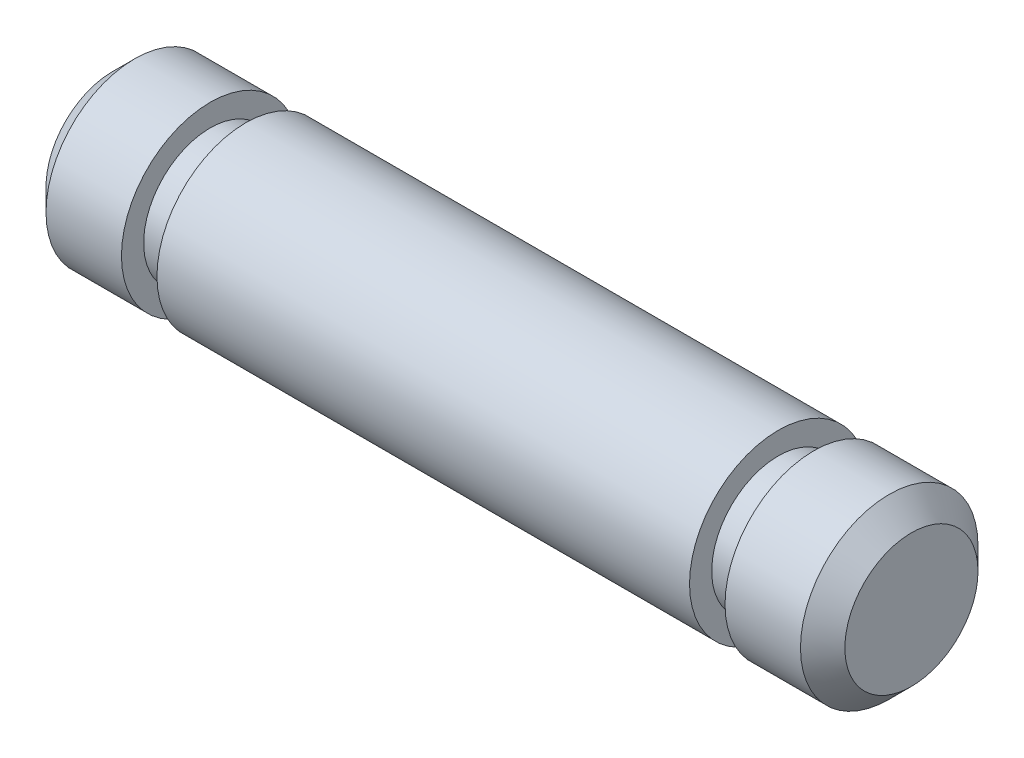
SolidWorks part; units mm, degrees
ref_plane "Front Plane" through (0, 0, 0) normal (0, 0, 1) x (1, 0, 0)
ref_plane "Top Plane" through (0, 0, 0) normal (0, 1, 0) x (1, 0, 0)
ref_plane "Right Plane" through (0, 0, 0) normal (1, 0, 0) x (0, 0, -1)
sketch "Sketch1" plane through (0, 0, 0) normal (1, 0, 0) x (0, 0, -1)
  circle A0 centre (0, 0) radius 2
  dimension "D1" = 4
extrude "Boss-Extrude1" add sketch "Sketch1" along normal mid plane 18
chamfer "Chamfer1" distance 0.5 angle 45 2 edges at (9, 0, -2) (-9, 0, -2)
sketch "Sketch2" plane through (9, 0, 0) normal (1, 0, 0) x (0, 0, -1)
  circle A0 centre (0, 0) radius 2 construction
  circle A1 centre (0, 0) radius 2
  circle A2 centre (0, 0) radius 1.5
  dimension "D1" = 3
extrude "Cut-Extrude1" cut sketch "Sketch2" along normal blind 0.8 from offset 3 offset against normal yes
mirror "Mirror1" about plane through (0, 0, 0) normal (1, 0, 0) of "Cut-Extrude1"
